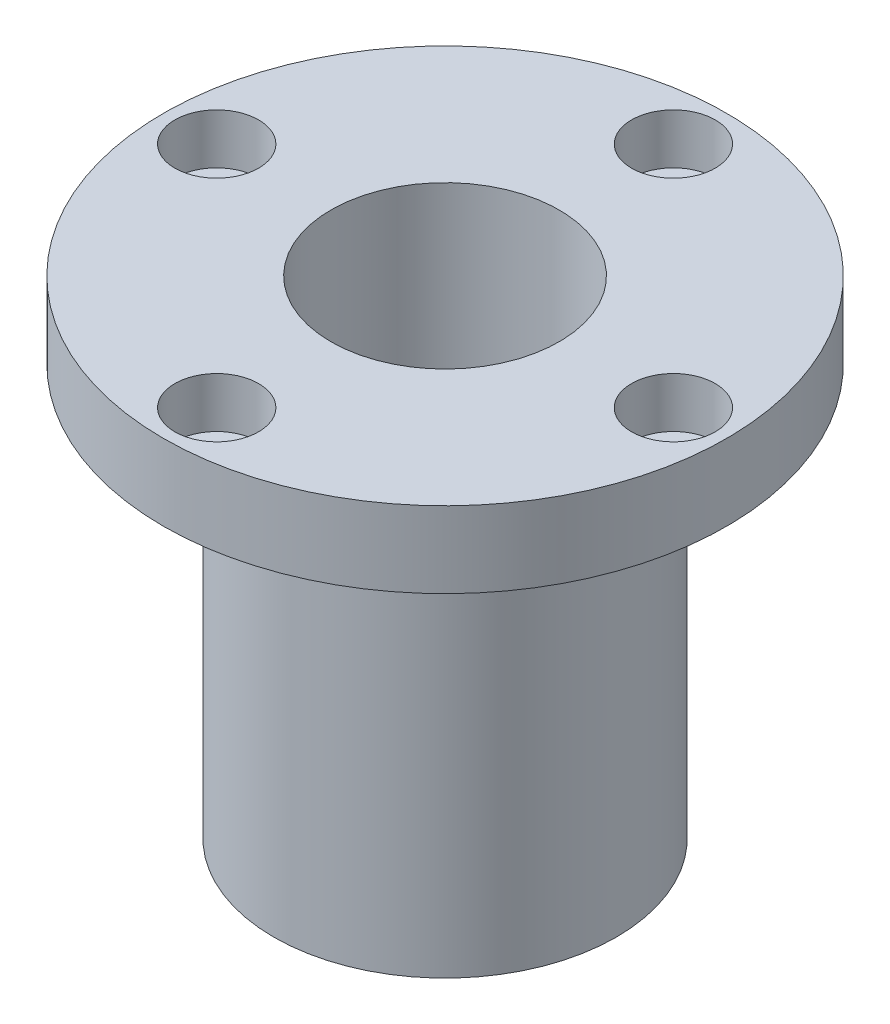
SolidWorks part; units mm, degrees
ref_plane "前视基准面" through (0, 0, 0) normal (0, 0, 1) x (1, 0, 0)
ref_plane "上视基准面" through (0, 0, 0) normal (0, 1, 0) x (1, 0, 0)
ref_plane "右视基准面" through (0, 0, 0) normal (1, 0, 0) x (0, 0, -1)
other "Configuration Table"
sketch "草图1" plane through (0, 0, 0) normal (0, 1, 0) x (1, 0, 0)
  circle A0 centre (0, 0) radius 22.5
  circle A1 centre (0, 0) radius 15
  dimension "D1" = 30
  dimension "D2" = 45
extrude "凸台-拉伸1" add sketch "草图1" along normal blind 64
sketch "草图2" plane through (0, 64, 0) normal (0, 1, 0) x (1, 0, 0)
  circle A0 centre (0, 0) radius 37
  circle A1 centre (0, 0) radius 22.5 construction
  circle A2 centre (0, 0) radius 22.5
  dimension "D1" = 74
extrude "凸台-拉伸2" add sketch "草图2" against normal blind 10
sketch "草图3" plane through (0, 64, 0) normal (0, 1, 0) x (1, 0, 0)
  circle A0 centre (0, 0) radius 30 construction
  circle A1 centre (0, 30) radius 5.5
  circle A2 centre (30, 0) radius 5.5
  circle A3 centre (0, -30) radius 5.5
  circle A4 centre (-30, 0) radius 5.5
  point P14 (0, 0)
  dimension "D1" = 60
  dimension "D2" = 11
  dimension "D3" = 4
extrude "切除-拉伸1" cut sketch "草图3" against normal blind 6.6
sketch "草图4" plane through (0, 64, 0) normal (0, 1, 0) x (1, 0, 0)
  circle A0 centre (0, 30) radius 5.5 construction
  circle A1 centre (0, 30) radius 5.5 construction
  circle A2 centre (0, 30) radius 3.3
  circle A3 centre (30, 0) radius 3.3
  circle A4 centre (0, -30) radius 3.3
  circle A5 centre (-30, 0) radius 3.3
  point P13 (0, 0)
  dimension "D1" = 6.6
  dimension "D2" = 4
extrude "切除-拉伸2" cut sketch "草图4" against normal through all
